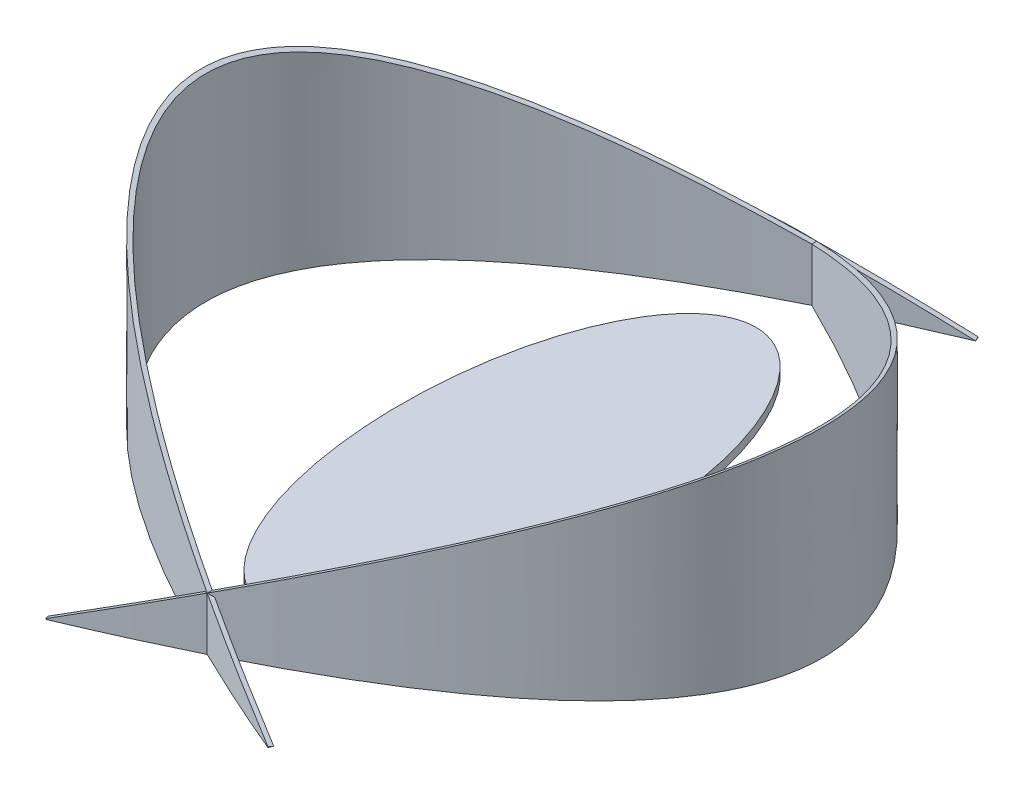
SolidWorks part; units mm, degrees
ref_plane "Front" through (0, 0, 0) normal (0, 0, 1) x (1, 0, 0)
ref_plane "Top" through (0, 0, 0) normal (0, 1, 0) x (1, 0, 0)
ref_plane "Right" through (0, 0, 0) normal (1, 0, 0) x (0, 0, -1)
sketch "Sketch1" plane through (0, 0, 0) normal (0, 1, 0) x (1, 0, 0)
  line L0 (25, 55) -> (-25, -55) construction
  line L1 (-25, 55) -> (25, 55) construction
  line L2 (-25, 55) -> (-25, -55) construction
  line L3 (-25, -55) -> (25, -55) construction
  line L4 (25, 55) -> (25, -55) construction
  ellipse E0 centre (0, 0) end of major axis (0, 55) minor radius 25
  dimension "D1" = 50
  dimension "D2" = 110
extrude "Extrude1" add sketch "Sketch1" along normal blind 2
sketch "Sketch2" plane through (0, 0, 0) normal (0, 1, 0) x (1, 0, 0)
  line L0 (-70, 0) -> (70, 0) construction
  line L1 (-25, -80) -> (-25, 80) construction
  line L2 (25, -80) -> (25, 80) construction
  line L3 (-25, -80) -> (25, -80) construction
  line L4 (-25, 80) -> (25, 80) construction
  line L5 (-76.8372, 80) -> (75.8295, 80) construction
  line L6 (-76.8372, -80) -> (75.8295, -80) construction
  line L7 (0, 80) -> (0, -80) construction
  line L8 (-70, -80) -> (-70, 80) construction
  line L9 (70, -80) -> (70, 80) construction
  line L10 (-76.8372, 0) -> (75.8295, 0) construction
  line L11 (-25.3881, 79.0784) -> (-25, 80)
  line L12 (-25.3881, -79.0784) -> (-25, -80)
  parabola Q0 (-25, 80) -> (-25, -80) focus (53.1579, 0) apex (70, 0)
  spline S0 degree 1 poles (-25.3881, 79.0784) (-25.3881, -79.0784) knots 0 0 1 1 construction
  spline S1 degree 3 poles (-25.3881, 79.0784) (-24.4068, 78.6652) (-22.437, 77.8293) (-18.5832, 76.1677) (-13.8742, 74.0875) (-8.4129, 71.5931) (-1.3783, 68.2674) (6.9492, 64.1117) (16.1972, 59.1275) (24.6997, 54.1465) (35.0418, 47.5109) (46.1037, 39.2294) (56.3909, 29.3258) (63.6958, 19.4768) (68.0417, 9.7039) (69.4791, 0) (68.0417, -9.7039) (63.6958, -19.4768) (56.3909, -29.3258) (46.1037, -39.2294) (35.0418, -47.5109) (24.6997, -54.1465) (16.1972, -59.1275) (6.9492, -64.1117) (-1.3783, -68.2674) (-8.4129, -71.5931) (-13.8742, -74.0875) (-18.5832, -76.1677) (-22.437, -77.8293) (-24.4068, -78.6652) (-25.3881, -79.0784) knots 0.489103 0.489103 0.489103 0.489103 0.489273 0.489443 0.489784 0.490124 0.490465 0.491146 0.491827 0.492508 0.493189 0.494551 0.495914 0.497276 0.498638 0.5 0.501362 0.502724 0.504086 0.505449 0.506811 0.507492 0.508173 0.508854 0.509535 0.509876 0.510216 0.510557 0.510727 0.510897 0.510897 0.510897 0.510897
  dimension "D1" = 25
  dimension "D2" = 70
  dimension "D3" = 45
  dimension "D5" = 80
extrude "Extrude2" add sketch "Sketch2" along normal blind 45 separate body
sketch "Sketch3" plane through (0, 0, 0) normal (0, 0, 1) x (1, 0, 0)
  line L0 (70, 45) -> (-25.3881, 45)
  line L1 (70, 45) -> (-25.3881, 0)
  line L2 (-25.3881, 45) -> (-25.3881, 0)
extrude "Cut-Extrude1" cut sketch "Sketch3" against normal mid plane 165
mirror "Mirror1" about plane through (0, 0, 0) normal (1, 0, 0) of bodies 103
